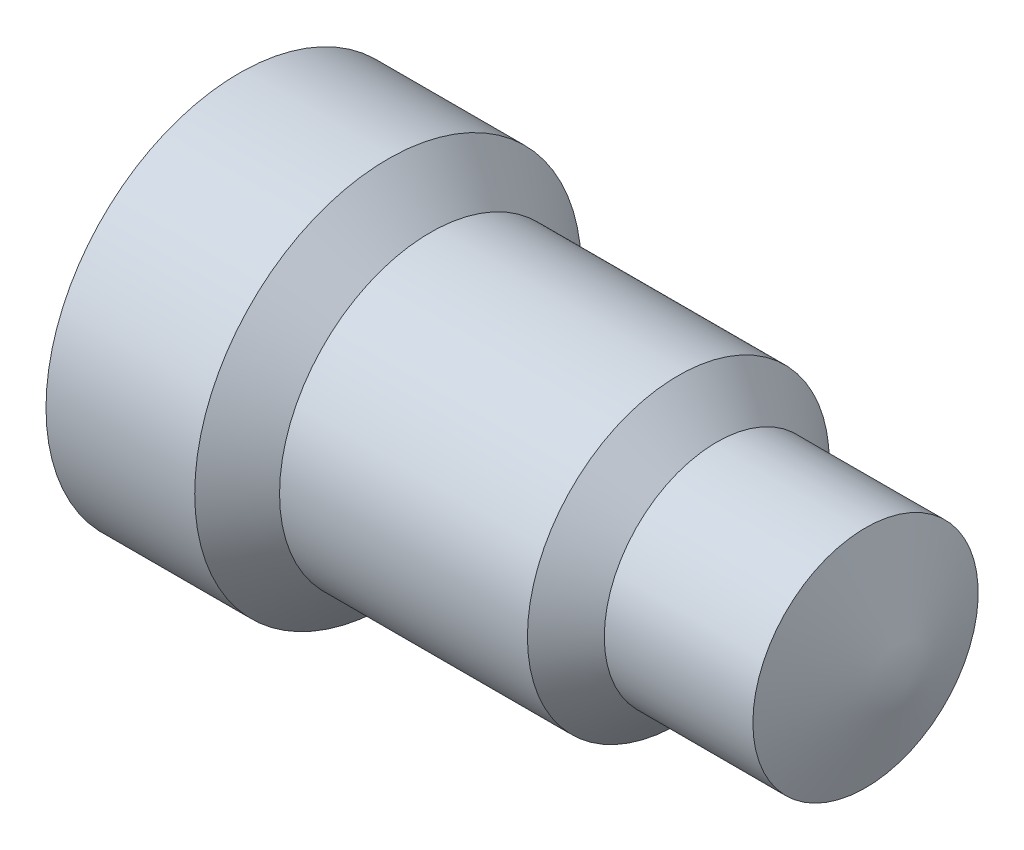
SolidWorks part; units mm, degrees
ref_plane "Front Plane" through (0, 0, 0) normal (0, 0, 1) x (1, 0, 0)
ref_plane "Top Plane" through (0, 0, 0) normal (0, 1, 0) x (1, 0, 0)
ref_plane "Right Plane" through (0, 0, 0) normal (1, 0, 0) x (0, 0, -1)
sketch "Sketch1" plane through (0, 0, 0) normal (0, 0, 1) x (1, 0, 0)
  line L0 (0, 0) -> (171.45, 0)
  line L2 (0, 0) -> (0, 49.53)
  line L3 (0, 49.53) -> (38.1, 49.53)
  line L11 (48.9762, 38.6743) -> (112.4762, 38.6743)
  line L12 (112.4762, 38.6743) -> (122.3222, 28.8283)
  line L13 (171.45, 0) -> (160.4222, 28.8585)
  line L14 (122.3222, 28.8283) -> (160.4222, 28.8585)
  line L15 (38.1, 49.53) -> (48.9762, 38.6743)
  dimension "D1" = 171.45
  dimension "D2" = 49.53
  dimension "D3" = 38.1
  dimension "D4" = 38.1
  dimension "D5" = 63.5
revolve "Revolve2" add sketch "Sketch1" angle 360 about L0
